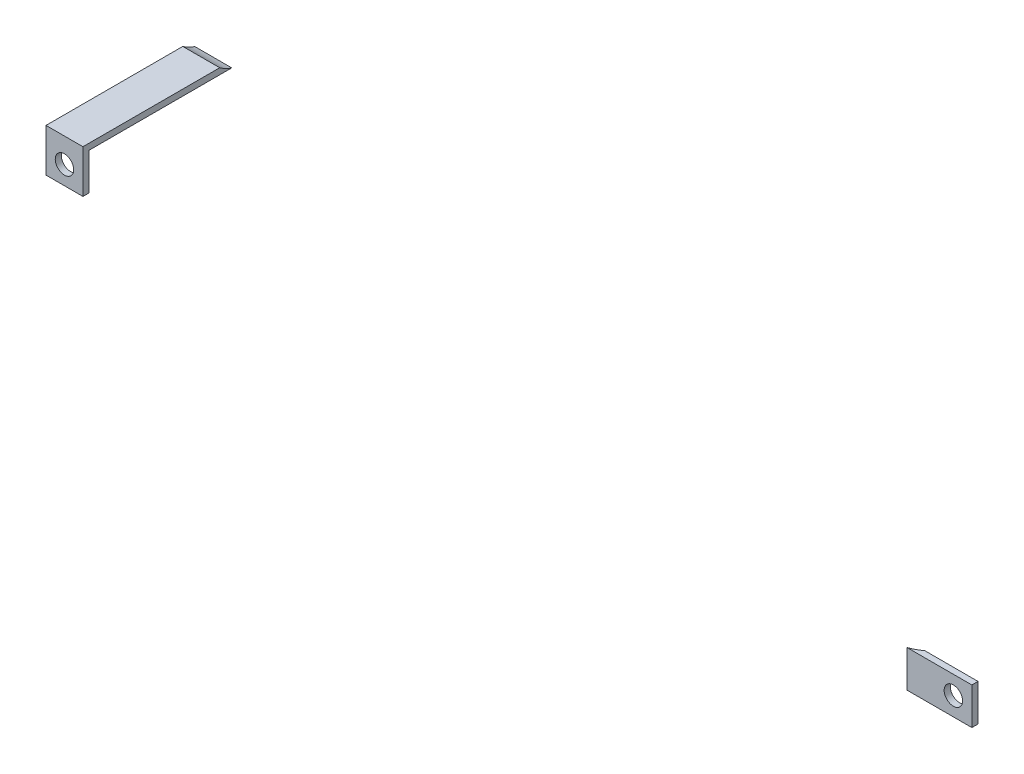
SolidWorks part; units mm, degrees
material "1.4113(X6CrMoS17-1)"
ref_plane "Płaszczyzna XY" through (0, 0, 0) normal (0, 0, 1) x (1, 0, 0)
ref_plane "Płaszczyzna XZ" through (0, 0, 0) normal (0, 1, 0) x (1, 0, 0)
ref_plane "Płaszczyzna YZ" through (0, 0, 0) normal (1, 0, 0) x (0, 0, -1)
ref_plane "Płaszczyzna2" through (0, 115, 0) normal (0, -1, 0) x (-1, 0, 0)
sketch "Szkic2" plane through (0, 115, 0) normal (0, -1, 0) x (-1, 0, 0)
  line L0 (-203.9399, -111) -> (-225, -111)
  line L1 (-225, -111) -> (-225, -109)
  line L2 (-225, -109) -> (-207.6851, -109)
  circle A0 centre (-200.0098, -99.1339) radius 12.5
  arc A1 (-207.6851, -109) -> (-203.9399, -111) centre (-200.0098, -99.1339) ccw
  dimension "D1" = 2
  dimension "D2" = 17.3149
  dimension "D3" = 21.0601
  dimension "D4" = 225
extrude "Dodanie-wyciągnięcie2" add sketch "Szkic2" against normal blind 12 separate body
ref_plane "Płaszczyzna3" through (0, 0, 109) normal (0, 0, -1) x (-1, 0, 0)
sketch "Szkic3" plane through (0, 0, 109) normal (0, 0, -1) x (-1, 0, 0)
  line L0 (-207.6851, 115) -> (-225, 115) construction
  line L2 (-225, 127) -> (-225, 115) construction
  circle A0 centre (-219, 121) radius 3
  dimension "D1" = 6
  dimension "D2" = 6
  dimension "D3" = 6
extrude "Wytnij-wyciągnięcie1" cut sketch "Szkic3" against normal blind 15
ref_plane "Płaszczyzna4" through (-34.852, 0, 0) normal (-1, 0, 0) x (0, 0, 1)
sketch "Szkic4" plane through (-34.852, 0, 0) normal (-1, 0, 0) x (0, 0, 1)
  line L0 (107.5535, 175.0403) -> (152, 175.0403)
  line L1 (152, 175.0403) -> (152, 161.0403)
  line L2 (152, 161.0403) -> (150, 161.0403)
  line L3 (150, 161.0403) -> (150, 173.0403)
  line L4 (150, 173.0403) -> (103.6354, 173.0403)
  spline S0 degree 3 poles (112.5, 185) (112.5, 160) (87.5, 160) (87.5, 185) (87.5, 210) (112.5, 210) (112.5, 185) (112.5, 160) (87.5, 160) knots -0.5 0 0 0 0.5 0.5 0.5 1 1 1 1.5 1.5 1.5 weights 1 0.333333 0.333333 1 0.333333 0.333333 1 0.333333 0.333333 only from (112.5, 185) to (112.5, 185)
  spline S1 degree 3 poles (107.5535, 175.0403) (106.3899, 174.1579) (105.0733, 173.4774) (103.6354, 173.0403) knots 0.165922 0.165922 0.165922 0.165922 0.212843 0.212843 0.212843 0.212843 weights 0.556553 0.535513 0.520344 0.511045
  dimension "D6" = 173.0403
  dimension "D1" = 2
  dimension "D2" = 14
  dimension "D3" = 12
  dimension "D4" = 152
  dimension "D5" = 175.0403
extrude "Dodanie-wyciągnięcie3" add sketch "Szkic4" against normal blind 12 separate body
ref_plane "Płaszczyzna5" through (0, 0, 150) normal (0, 0, -1) x (-1, 0, 0)
sketch "Szkic5" plane through (0, 0, 150) normal (0, 0, -1) x (-1, 0, 0)
  line L0 (22.852, 161.0403) -> (34.852, 161.0403) construction
  line L1 (22.852, 173.0403) -> (22.852, 161.0403) construction
  circle A0 centre (28.852, 167.0403) radius 3
  dimension "D1" = 6
  dimension "D2" = 6
  dimension "D3" = 6
extrude "Wytnij-wyciągnięcie2" cut sketch "Szkic5" against normal blind 12
